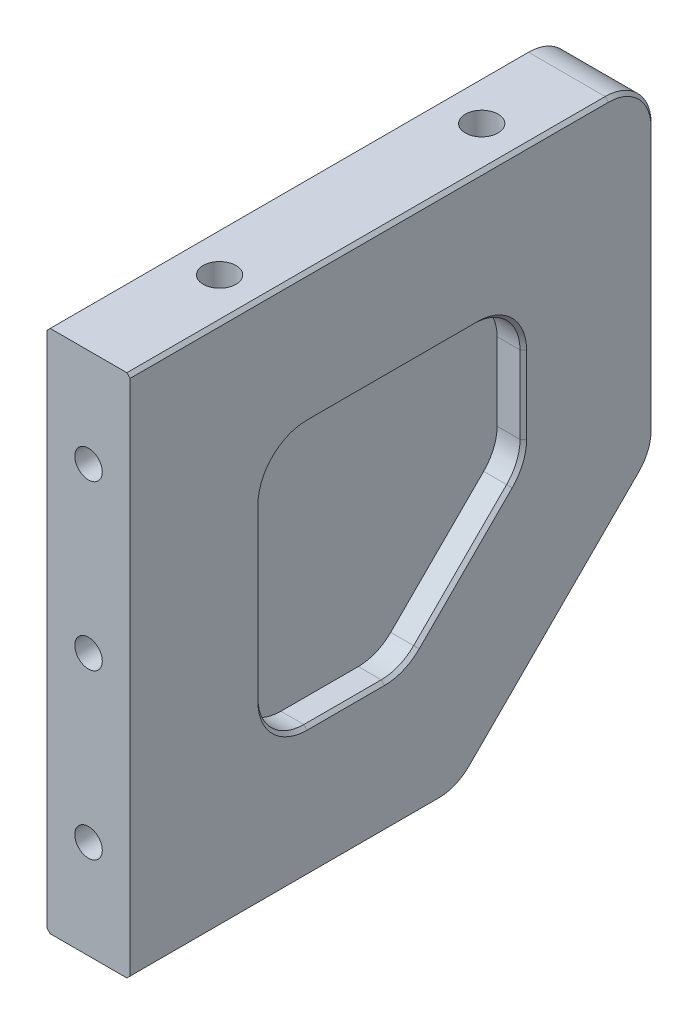
SolidWorks part; units mm, degrees
ref_plane "Front Plane" through (0, 0, 0) normal (0, 0, 1) x (1, 0, 0)
ref_plane "Top Plane" through (0, 0, 0) normal (0, 1, 0) x (1, 0, 0)
ref_plane "Right Plane" through (0, 0, 0) normal (1, 0, 0) x (0, 0, -1)
sketch "Sketch1" plane through (0, 0, 0) normal (1, 0, 0) x (0, 0, -1)
  line L1 (40, -40) -> (-40, -40)
  line L2 (40, -40) -> (40, 40)
  line L3 (40, 40) -> (-40, 40)
  line L4 (-40, -40) -> (-40, 40)
  line L5 (40, -40) -> (-40, 40) construction
  line L6 (40, 40) -> (-40, -40) construction
  point P0 (0, 0)
  dimension "D1" = 80
extrude "Boss-Extrude1" add sketch "Sketch1" along normal mid plane 12.7
chamfer "Chamfer1" distance 30 angle 45 1 edges at (0, -40, -40)
sketch "Sketch2" plane through (0, 40, 0) normal (0, 1, 0) x (1, 0, 0)
  line L0 (0, -20) -> (0, -40) construction
  line L1 (6.35, 40) -> (-6.35, 40) construction
  line L3 (0, 20) -> (0, 40) construction
  line L4 (6.35, -40) -> (-6.35, -40) construction
  circle A0 centre (0, 20) radius 2.5
  circle A1 centre (0, -20) radius 2.5
  dimension "D2" = 5
  dimension "D1" = 40
extrude "Cut-Extrude1" cut sketch "Sketch2" against normal blind 17
sketch "Sketch3" plane through (0, 0, 40) normal (0, 0, 1) x (1, 0, 0)
  line L0 (0, 40) -> (0, 25) construction
  line L1 (6.35, 40) -> (-6.35, 40) construction
  line L2 (0, 25) -> (0, 0) construction
  line L3 (0, -25) -> (0, -40) construction
  line L4 (6.35, -40) -> (-6.35, -40) construction
  line L5 (0, 0) -> (0, -25) construction
  line L6 (-6.35, 0) -> (0, 0) construction
  line L7 (-6.35, 40) -> (-6.35, -40) construction
  circle A0 centre (0, 25) radius 2.1
  circle A1 centre (0, -25) radius 2.1
  circle A2 centre (0, 0) radius 2.1
  dimension "D1" = 4.2
  dimension "D2" = 15
extrude "Cut-Extrude2" cut sketch "Sketch3" against normal blind 15
sketch "Sketch4" plane through (6.35, 0, 0) normal (1, 0, 0) x (0, 0, -1)
  line L12 (-20, -20) -> (1.7157, -20)
  line L13 (1.7157, -20) -> (20, -1.7157)
  line L14 (20, -1.7157) -> (20, 20)
  line L15 (20, 20) -> (-20, 20)
  line L16 (-20, 20) -> (-20, -20)
  line L17 (-20, -20) -> (1.7157, -20)
  line L18 (1.7157, -20) -> (20, -1.7157)
  line L19 (20, -1.7157) -> (20, 20)
  line L20 (20, 20) -> (-20, 20)
  line L21 (-20, 20) -> (-20, -20)
  dimension "D1" = 20
extrude "Cut-Extrude3" cut sketch "Sketch4" against normal blind 4
fillet "Fillet1" radius 7 5 edges at (4.35, -20, 20) (4.35, -20, -1.7157) (4.35, 20, -20) (4.35, 20, 20) (4.35, -1.7157, -20)
mirror "Mirror2" about plane through (0, 0, 0) normal (1, 0, 0) of "Fillet1", "Cut-Extrude3"
fillet "Fillet2" radius 7 3 edges at (0, -40, -10) (0, -10, -40) (0, 40, -40)
chamfer "Chamfer2" distance 0.5 angle 45 34 edges at (-6.35, -40, 16.4497) (-6.35, -39.4672, -9.7793) (-6.35, -25, -25) (-6.35, -9.7793, -39.4672) (-6.35, 12.9497, -40) (-6.35, 37.9497, -37.9497) (-6.35, 40, 3.5) (-6.35, -10.8579, -10.8579) (-6.35, -1.495, -19.4672) (-6.35, -19.4672, -1.495) (-6.35, 7.0919, -20) (-6.35, -20, 7.0919) (-6.35, 17.9497, -17.9497) (-6.35, -17.9497, 17.9497) (-6.35, 20, 0) (-6.35, 0, 20) (-6.35, 17.9497, 17.9497) (6.35, -40, 16.4497) (6.35, -39.4672, -9.7793) (6.35, -25, -25) (6.35, 40, 3.5) (6.35, -9.7793, -39.4672) (6.35, 37.9497, -37.9497) (6.35, 12.9497, -40) (6.35, -1.495, -19.4672) (6.35, 7.0919, -20) (6.35, -10.8579, -10.8579) (6.35, 17.9497, -17.9497) (6.35, -19.4672, -1.495) (6.35, 20, 0) (6.35, -20, 7.0919) (6.35, 17.9497, 17.9497) (6.35, -17.9497, 17.9497) (6.35, 0, 20)
